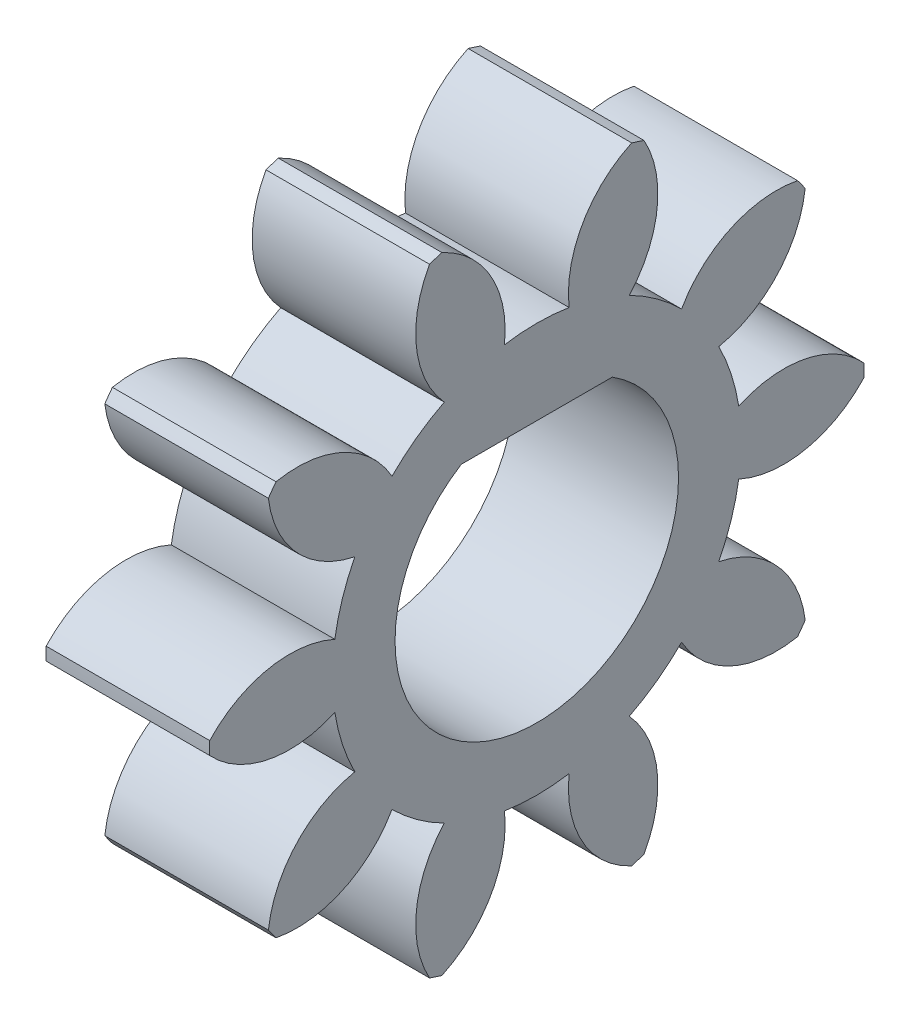
SolidWorks part; units mm, degrees
ref_plane "Plane1" through (0, 0, 0) normal (0, 0, 1) x (1, 0, 0)
ref_plane "Plane2" through (0, 0, 0) normal (0, 1, 0) x (1, 0, 0)
ref_plane "Plane3" through (0, 0, 0) normal (1, 0, 0) x (0, 0, -1)
other "Configuration Table"
sketch "HoldingSke" plane through (0, 0, 0) normal (0, 1, 0) x (1, 0, 0)
  line L0 (0, 0) -> (0.9848, -0.1736)
  line L1 (-15, 0) -> (100, 0) construction
  line L2 (0, 0) -> (-2.1039, 2.3779)
  line L3 (0, 0) -> (-11.863, 4.5341)
  line L4 (0, 0) -> (8.5048, 1.4996)
  line L5 (0, 0) -> (-46.8476, -17.4728)
  line L6 (0, 0) -> (-8.2896, -5.593)
  line L7 (-2.1039, 2.3779) -> (8.6586, 51.2059)
  line L8 (-76.2, 54.61) -> (-75.3, 54.61)
  line L9 (-71.009, 38.7566) -> (-53.1078, 45.2721)
  line L10 (-76.2, 71.12) -> (104.1128, 71.12)
  line L11 (0, 0) -> (-10, 0)
  line L12 (-76.2, 101.6) -> (-76.162, 101.6)
  line L13 (24.9733, 27.94) -> (52.9518, 28.4284)
  line L14 (24.9733, 27.94) -> (24.9743, 27.94)
  line L15 (24.9733, 27.94) -> (100.4006, 29.5858)
  line L16 (-63.627, -1) -> (-12.827, -1)
  circle A0 centre (0, 0) radius 2.5
  circle A1 centre (0, 0) radius 3.749
  circle A2 centre (0, 0) radius 37.5
  circle A3 centre (0, 0) radius 2.5
  dimension "MHD" = 7.498
  dimension "Hub_dia" = 75
  dimension "Bore" = 5
  dimension "MBD" = 5
  dimension "Num_teeth" = 10
  dimension "Pitch" = 1
  dimension "Overall_len" = 50
  dimension "Show_teeth" = 10
  dimension "Thickness" = 10
  dimension "OAL" = 50.0001
  dimension "T_dim" = 0.9
  dimension "Ap" = 20
  dimension "H" = 19.05
  dimension "Pitch_radius" = 180.3128
  dimension "Width" = 10
  dimension "Backlash" = 0.038
  dimension "Addendum_fac" = 1
  dimension "Dedendum_fac" = 1.25
  dimension "Clearance_fac" = 0.25
  dimension "Dedendum_add" = 0.001
  dimension "Module" = 1
sketch "BasProSke" plane through (0, 0, 0) normal (0, 1, 0) x (1, 0, 0)
  line L0 (-10, 0) -> (60, 0) construction
  line L1 (0, 0) -> (0, 6)
  line L2 (0, 0) -> (10, 0)
  line L3 (10, 0) -> (10, 6)
  line L4 (10, 6) -> (0, 6)
  dimension "Thickness" = 10
  dimension "Diameter" = 12
revolve "Base-Revolve" add sketch "BasProSke" angle 360 about L0
sketch "TooCutSke" plane through (0, 0, 0) normal (1, 0, 0) x (0, 0, -1)
  line L1 (0, 0) -> (0, 107) construction
  line L2 (0, 0) -> (-0.8485, 4.9275) construction
  line L3 (0, 0) -> (-3.0584, 9.4126) construction
  line L4 (-0.8485, 4.9275) -> (-1.5292, 4.7063) construction
  arc A0 (0.5928, 3.7018) -> (-0.5928, 3.7018) centre (0, 0) ccw
  arc A1 (1.7758, 5.7578) -> (-1.7758, 5.7578) centre (0, 0) ccw
  circle A2 centre (0, 0) radius 5 construction
  circle A3 centre (0, 0) radius 4.6985 construction
  arc A4 (-0.5928, 3.7018) -> (-1.7758, 5.7578) centre (-2.5801, 3.9267) ccw
  arc A5 (1.7758, 5.7578) -> (0.5928, 3.7018) centre (2.5801, 3.9267) ccw
  dimension "Root_dia" = 7.498
  dimension "Overcut_dia" = 12.0508
  dimension "Pitch_dia" = 10
  dimension "Base_dia" = 9.3969
  dimension "Flank_rad" = 2
  dimension "Half_ang" = 18
  dimension "Half_CT" = 0.7157
extrude "ToothCut" cut sketch "TooCutSke" along normal through all
fillet "Breaks" [suppressed] radius 0.02
fillet "RootFillets" [suppressed] radius 0.251
pattern_circular "TeethCuts" count 10 every 36 about axis through (-10, 0, 0) along (1, 0, 0) of "ToothCut", "RootFillets", "Breaks"
sketch "HubNeaOneSke" plane through (0, 0, 0) normal (-1, 0, 0) x (0, 0, 1)
  circle A0 centre (0, 0) radius 3.749
  dimension "Diameter" = 7.498
extrude "HubNearOne" [suppressed] add sketch "HubNeaOneSke" along normal blind 40.0001
sketch "HubNeaBotSke" plane through (0, 0, 0) normal (-1, 0, 0) x (0, 0, 1)
  circle A0 centre (0, 0) radius 3.749
  dimension "Diameter" = 7.498
extrude "HubNearBoth" [suppressed] add sketch "HubNeaBotSke" along normal blind 20
ref_plane "FarPln" through (10, 0, 0) normal (1, 0, 0) x (0, 0, -1)
sketch "HubFarSke" plane through (10, 0, 0) normal (1, 0, 0) x (0, 0, -1)
  circle A0 centre (0, 0) radius 3.749
  dimension "Diameter" = 7.498
extrude "HubFar" [suppressed] add sketch "HubFarSke" along normal blind 20
sketch "BorSke" plane through (0, 0, 0) normal (1, 0, 0) x (0, 0, -1)
  circle A0 centre (0, 0) radius 2.5
  dimension "Diameter" = 5
extrude "Bore" cut sketch "BorSke" along normal mid plane 100.0001
sketch "KeySke" plane through (0, 0, 0) normal (1, 0, 0) x (0, 0, -1)
  line L0 (-1, 0) -> (-1, 3.4)
  line L1 (-1, 3.4) -> (1, 3.4)
  line L2 (1, 3.4) -> (1, 0)
  line L3 (0, 0) -> (0, 34) construction
  line L4 (-1, 0) -> (1, 0)
  dimension "Offset" = 3.4
  dimension "Width" = 2
extrude "Keyway" [suppressed] cut sketch "KeySke" along normal mid plane 100.0001
pattern_circular "Keyway2" [suppressed] count 2 every 90 about axis through (-10, 0, 0) along (1, 0, 0)
sketch "Sketch1" plane through (10, 0, 0) normal (1, 0, 0) x (0, 0, -1)
  line L0 (0, 0) -> (2.4, 0) construction
  line L1 (2.4, 0.7) -> (2.4, -0.7) construction
  circle A0 centre (0, 0) radius 2.5
  point P7 (2.4, 0)
extrude "Boss-Extrude1" add sketch "Sketch1" against normal blind 10
sketch "Sketch2" plane through (0, 0, 0) normal (-1, 0, 0) x (0, 0, 1)
  line L0 (0, 0) -> (0, 2.2) construction
  line L1 (-1.1874, 2.2) -> (1.1874, 2.2)
  circle A0 centre (0, 0) radius 2.5
  point P7 (0, 2.2)
extrude "Cut-Extrude2" cut sketch "Sketch2" against normal blind 10
sketch "Sketch3" plane through (0, 0, 0) normal (-1, 0, 0) x (0, 0, 1)
  line L0 (-1.3856, 2.2) -> (1.3856, 2.2)
  arc A0 (-1.1874, 2.2) -> (1.1874, 2.2) centre (0, 0) ccw construction
  arc A1 (-1.1874, 2.2) -> (1.1874, 2.2) centre (0, 0) ccw
  arc A2 (-1.3856, 2.2) -> (1.3856, 2.2) centre (0, 0) ccw
  arc A3 (-1.2349, 2.288) -> (1.2349, 2.288) centre (0, 0) ccw construction
  point P9 (0, 2.2)
  dimension "D1" = 0.1
extrude "Cut-Extrude4" cut sketch "Sketch3" against normal blind 12.8 contours A2 L0
sketch "Sketch4" plane through (10, 0, 0) normal (1, 0, 0) x (0, 0, -1)
  arc A40 (5.9988, 0.1189) -> (3.7038, 0.5802) centre (4.5318, -1.2404) ccw
  arc A41 (3.7038, 0.5802) -> (3.3375, 1.7077) centre (0, 0) ccw
  arc A42 (3.3375, 1.7077) -> (4.923, 3.4298) centre (2.9372, 3.6672) ccw
  arc A43 (4.923, 3.4298) -> (4.7833, 3.6222) centre (0, 0) ccw
  arc A44 (4.7833, 3.6222) -> (2.6555, 2.6464) centre (4.3954, 1.6602) ccw
  arc A45 (2.6555, 2.6464) -> (1.6963, 3.3433) centre (0, 0) ccw
  arc A46 (1.6963, 3.3433) -> (1.9668, 5.6685) centre (0.2207, 4.6933) ccw
  arc A47 (1.9668, 5.6685) -> (1.7407, 5.742) centre (0, 0) ccw
  arc A48 (1.7407, 5.742) -> (0.5928, 3.7018) centre (2.5801, 3.9267) ccw
  arc A49 (0.5928, 3.7018) -> (-0.5928, 3.7018) centre (0, 0) ccw
  arc A50 (-0.5928, 3.7018) -> (-1.7407, 5.742) centre (-2.5801, 3.9267) ccw
  arc A51 (-1.7407, 5.742) -> (-1.9668, 5.6685) centre (0, 0) ccw
  arc A52 (-1.9668, 5.6685) -> (-1.6963, 3.3433) centre (-0.2207, 4.6933) ccw
  arc A53 (-1.6963, 3.3433) -> (-2.6555, 2.6464) centre (0, 0) ccw
  arc A54 (-2.6555, 2.6464) -> (-4.7833, 3.6222) centre (-4.3954, 1.6602) ccw
  arc A55 (-4.7833, 3.6222) -> (-4.923, 3.4298) centre (0, 0) ccw
  arc A56 (-4.923, 3.4298) -> (-3.3375, 1.7077) centre (-2.9372, 3.6672) ccw
  arc A57 (-3.3375, 1.7077) -> (-3.7038, 0.5802) centre (0, 0) ccw
  arc A58 (-3.7038, 0.5802) -> (-5.9988, 0.1189) centre (-4.5318, -1.2404) ccw
  arc A59 (-5.9988, 0.1189) -> (-5.9988, -0.1189) centre (0, 0) ccw
  arc A60 (-5.9988, -0.1189) -> (-3.7038, -0.5802) centre (-4.5318, 1.2404) ccw
  arc A61 (-3.7038, -0.5802) -> (-3.3375, -1.7077) centre (0, 0) ccw
  arc A62 (-3.3375, -1.7077) -> (-4.923, -3.4298) centre (-2.9372, -3.6672) ccw
  arc A63 (-4.923, -3.4298) -> (-4.7833, -3.6222) centre (0, 0) ccw
  arc A64 (-4.7833, -3.6222) -> (-2.6555, -2.6464) centre (-4.3954, -1.6602) ccw
  arc A65 (-2.6555, -2.6464) -> (-1.6963, -3.3433) centre (0, 0) ccw
  arc A66 (-1.6963, -3.3433) -> (-1.9668, -5.6685) centre (-0.2207, -4.6933) ccw
  arc A67 (-1.9668, -5.6685) -> (-1.7407, -5.742) centre (0, 0) ccw
  arc A68 (-1.7407, -5.742) -> (-0.5928, -3.7018) centre (-2.5801, -3.9267) ccw
  arc A69 (-0.5928, -3.7018) -> (0.5928, -3.7018) centre (0, 0) ccw
  arc A70 (0.5928, -3.7018) -> (1.7407, -5.742) centre (2.5801, -3.9267) ccw
  arc A71 (1.7407, -5.742) -> (1.9668, -5.6685) centre (0, 0) ccw
  arc A72 (1.9668, -5.6685) -> (1.6963, -3.3433) centre (0.2207, -4.6933) ccw
  arc A73 (1.6963, -3.3433) -> (2.6555, -2.6464) centre (0, 0) ccw
  arc A74 (2.6555, -2.6464) -> (4.7833, -3.6222) centre (4.3954, -1.6602) ccw
  arc A75 (4.7833, -3.6222) -> (4.923, -3.4298) centre (0, 0) ccw
  arc A76 (4.923, -3.4298) -> (3.3375, -1.7077) centre (2.9372, -3.6672) ccw
  arc A77 (3.3375, -1.7077) -> (3.7038, -0.5802) centre (0, 0) ccw
  arc A78 (3.7038, -0.5802) -> (5.9988, -0.1189) centre (4.5318, 1.2404) ccw
  arc A79 (5.9988, -0.1189) -> (5.9988, 0.1189) centre (0, 0) ccw
  arc A80 (5.9988, 0.1189) -> (3.7038, 0.5802) centre (4.5318, -1.2404) ccw
  arc A81 (3.7038, 0.5802) -> (3.3375, 1.7077) centre (0, 0) ccw
  arc A82 (3.3375, 1.7077) -> (4.923, 3.4298) centre (2.9372, 3.6672) ccw
  arc A83 (4.923, 3.4298) -> (4.7833, 3.6222) centre (0, 0) ccw
  arc A84 (4.7833, 3.6222) -> (2.6555, 2.6464) centre (4.3954, 1.6602) ccw
  arc A85 (2.6555, 2.6464) -> (1.6963, 3.3433) centre (0, 0) ccw
  arc A86 (1.6963, 3.3433) -> (1.9668, 5.6685) centre (0.2207, 4.6933) ccw
  arc A87 (1.9668, 5.6685) -> (1.7407, 5.742) centre (0, 0) ccw
  arc A88 (1.7407, 5.742) -> (0.5928, 3.7018) centre (2.5801, 3.9267) ccw
  arc A89 (0.5928, 3.7018) -> (-0.5928, 3.7018) centre (0, 0) ccw
  arc A90 (-0.5928, 3.7018) -> (-1.7407, 5.742) centre (-2.5801, 3.9267) ccw
  arc A91 (-1.7407, 5.742) -> (-1.9668, 5.6685) centre (0, 0) ccw
  arc A92 (-1.9668, 5.6685) -> (-1.6963, 3.3433) centre (-0.2207, 4.6933) ccw
  arc A93 (-1.6963, 3.3433) -> (-2.6555, 2.6464) centre (0, 0) ccw
  arc A94 (-2.6555, 2.6464) -> (-4.7833, 3.6222) centre (-4.3954, 1.6602) ccw
  arc A95 (-4.7833, 3.6222) -> (-4.923, 3.4298) centre (0, 0) ccw
  arc A96 (-4.923, 3.4298) -> (-3.3375, 1.7077) centre (-2.9372, 3.6672) ccw
  arc A97 (-3.3375, 1.7077) -> (-3.7038, 0.5802) centre (0, 0) ccw
  arc A98 (-3.7038, 0.5802) -> (-5.9988, 0.1189) centre (-4.5318, -1.2404) ccw
  arc A99 (-5.9988, 0.1189) -> (-5.9988, -0.1189) centre (0, 0) ccw
  arc A100 (-5.9988, -0.1189) -> (-3.7038, -0.5802) centre (-4.5318, 1.2404) ccw
  arc A101 (-3.7038, -0.5802) -> (-3.3375, -1.7077) centre (0, 0) ccw
  arc A102 (-3.3375, -1.7077) -> (-4.923, -3.4298) centre (-2.9372, -3.6672) ccw
  arc A103 (-4.923, -3.4298) -> (-4.7833, -3.6222) centre (0, 0) ccw
  arc A104 (-4.7833, -3.6222) -> (-2.6555, -2.6464) centre (-4.3954, -1.6602) ccw
  arc A105 (-2.6555, -2.6464) -> (-1.6963, -3.3433) centre (0, 0) ccw
  arc A106 (-1.6963, -3.3433) -> (-1.9668, -5.6685) centre (-0.2207, -4.6933) ccw
  arc A107 (-1.9668, -5.6685) -> (-1.7407, -5.742) centre (0, 0) ccw
  arc A108 (-1.7407, -5.742) -> (-0.5928, -3.7018) centre (-2.5801, -3.9267) ccw
  arc A109 (-0.5928, -3.7018) -> (0.5928, -3.7018) centre (0, 0) ccw
  arc A110 (0.5928, -3.7018) -> (1.7407, -5.742) centre (2.5801, -3.9267) ccw
  arc A111 (1.7407, -5.742) -> (1.9668, -5.6685) centre (0, 0) ccw
  arc A112 (1.9668, -5.6685) -> (1.6963, -3.3433) centre (0.2207, -4.6933) ccw
  arc A113 (1.6963, -3.3433) -> (2.6555, -2.6464) centre (0, 0) ccw
  arc A114 (2.6555, -2.6464) -> (4.7833, -3.6222) centre (4.3954, -1.6602) ccw
  arc A115 (4.7833, -3.6222) -> (4.923, -3.4298) centre (0, 0) ccw
  arc A116 (4.923, -3.4298) -> (3.3375, -1.7077) centre (2.9372, -3.6672) ccw
  arc A117 (3.3375, -1.7077) -> (3.7038, -0.5802) centre (0, 0) ccw
  arc A118 (3.7038, -0.5802) -> (5.9988, -0.1189) centre (4.5318, 1.2404) ccw
  arc A119 (5.9988, -0.1189) -> (5.9988, 0.1189) centre (0, 0) ccw
  dimension "D1" = 0
extrude "Cut-Extrude5" cut sketch "Sketch4" against normal blind 7 contours A80 A81 A82 A83 A84 A85 A86 A87 A88 A89 A90 A91 A92 A93 A94 A95 A96 A97 A98 A99 A100 A101 A102 A103 A104 A105 A106 A107 A108 A109 A110 A111 A112 A113 A114 A115 A116 A117 A118 A119
equation "' \"Module@HoldingSke\" = 6.35"
equation "' \"Num_teeth@HoldingSke\" = 12"
equation "' \"Ap@HoldingSke\" =  20"
equation "' \"Ap@HoldingSke\" = 20"
equation "' \"Width@HoldingSke\" = 0.5 * 25.4"
equation "' \"Hub_dia@HoldingSke\"= 1 * 25.4"
equation "' \"Hub_dia@HoldingSke\" = 1 * 25.4"
equation "' \"Overall_len@HoldingSke\" = 1.0 * 25.4"
equation "' \"Bore@HoldingSke\" = 0.75 * 25.4"
equation "' \"T_dim@HoldingSke\" = 0.1 * 25.4"
equation "' \"Width@KeySke\" = 0.25 * 25.4"
equation "' \"Show_teeth@HoldingSke\" = 13"
equation "' \"Backlash@HoldingSke\" = 0.009 * 25.4"
equation "' \"Addendum_fac@HoldingSke\" = 1.0"
equation "' \"Dedendum_fac@HoldingSke\" = 1.25"
equation "' \"Dedendum_add@HoldingSke\" = 0.00005 * 25.4"
equation "' \"Clearance_fac@HoldingSke\" = 0.25"
equation "\"Pitch@HoldingSke\" = 1 / \"Module@HoldingSke\""
equation "\"Overcut_dia@TooCutSke\" = (\"Num_teeth@HoldingSke\" + 2 * \"Addendum_fac@HoldingSke\") / \"Pitch@HoldingSke\" + 0.002 * 25.4"
equation "\"Pitch_dia@TooCutSke\" = \"Num_teeth@HoldingSke\" / \"Pitch@HoldingSke\""
equation "\"Base_dia@TooCutSke\" = \"Num_teeth@HoldingSke\" / \"Pitch@HoldingSke\" * cos((\"Ap@HoldingSke\"  * 3.14159265 / 180))"
equation "\"Root_dia@TooCutSke\" = (\"Num_teeth@HoldingSke\" + 2) / \"Pitch@HoldingSke\" - 2 * (\"Addendum_fac@HoldingSke\" + \"Dedendum_fac@HoldingSke\") / \"Pitch@HoldingSke\" - \"Dedendum_add@HoldingSke\" * 2"
equation "\"Half_ang@TooCutSke\" = 180 / \"Num_teeth@HoldingSke\""
equation "\"Half_CT@TooCutSke\" = \"Num_teeth@HoldingSke\" / \"Pitch@HoldingSke\" * sin((3.14159265 / 2 / \"Num_teeth@HoldingSke\")) / 2 - 7 * \"Backlash@HoldingSke\" / 4"
equation "\"Flank_rad@TooCutSke\" = \"Num_teeth@HoldingSke\" / \"Pitch@HoldingSke\" / 5"
equation "\"Radius@RootFillets\" = \"Clearance_fac@HoldingSke\" / \"Pitch@HoldingSke\" + \"Dedendum_add@HoldingSke\""
equation "\"Break_rad@Breaks\" = 0.02 / \"Pitch@HoldingSke\""
equation "\"Thickness@HoldingSke\" = \"Width@HoldingSke\""
equation "\"OAL@HoldingSke\" = \"Thickness@HoldingSke\""
equation "\"MHD@HoldingSke\" = (\"Num_teeth@HoldingSke\" + 2) / \"Pitch@HoldingSke\" - 2 * (\"Addendum_fac@HoldingSke\" + \"Dedendum_fac@HoldingSke\")  / \"Pitch@HoldingSke\" - \"Dedendum_add@HoldingSke\" * 2"
equation "\"MBD@HoldingSke\" = (\"Num_teeth@HoldingSke\" + 2) / \"Pitch@HoldingSke\" - 2 * (\"Addendum_fac@HoldingSke\" + \"Dedendum_fac@HoldingSke\")  / \"Pitch@HoldingSke\" - \"Dedendum_add@HoldingSke\" * 2 - 0.002 * 25.4"
equation "\"MHD@HoldingSke\" = ((sgn( \"MHD@HoldingSke\" - \"Hub_dia@HoldingSke\" )-1)*( \"MHD@HoldingSke\" - \"Hub_dia@HoldingSke\" ))/-2+ \"Hub_dia@HoldingSke\""
equation "\"MBD@HoldingSke\" = ((sgn( \"MBD@HoldingSke\" - \"Bore@HoldingSke\" )-1)*( \"MBD@HoldingSke\" - \"Bore@HoldingSke\" ))/-2+ \"Bore@HoldingSke\""
equation "\"OAL@HoldingSke\" = ((sgn( \"OAL@HoldingSke\" - \"Overall_len@HoldingSke\" )+1)*( \"OAL@HoldingSke\" - \"Overall_len@HoldingSke\" ))/2 + \"Overall_len@HoldingSke\" + 0.000002 * 25.4"
equation "\"Num_teeth@TeethCuts\" = int( \"Show_teeth@HoldingSke\" ) + 1"
equation "\"Num_teeth@TeethCuts\" = ((sgn( \"Num_teeth@TeethCuts\" - \"Num_teeth@HoldingSke\" )-1)*( \"Num_teeth@TeethCuts\" - \"Num_teeth@HoldingSke\" ))/-2+ \"Num_teeth@HoldingSke\""
equation "\"Num_teeth@TeethCuts\" = ((sgn( \"Num_teeth@TeethCuts\" - 2.0)+1)*( \"Num_teeth@TeethCuts\" - 2.0))/2 +2.0"
equation "\"Angle@TeethCuts\" = 360.0 / \"Num_teeth@HoldingSke\""
equation "\"Diameter@BasProSke\" = (\"Num_teeth@HoldingSke\" + 2 * \"Addendum_fac@HoldingSke\") / \"Pitch@HoldingSke\""
equation "\"Thickness@BasProSke\"  = \"Thickness@HoldingSke\""
equation "' \"Fillet_rad@BasProSke\" =  \"Thickness@HoldingSke\" * 0.05"
equation "' \"Fillet_rad@BasProSke\" = \"Thickness@HoldingSke\" * 0.05"
equation "\"MHD@HoldingSke\" = ((sgn( \"MHD@HoldingSke\" - \"Root_dia@TooCutSke\" )-1)*( \"MHD@HoldingSke\" - \"Root_dia@TooCutSke\" ))/-2+ \"Root_dia@TooCutSke\""
equation "\"Diameter@HubNeaOneSke\" = \"MHD@HoldingSke\""
equation "\"Length@HubNearOne\" = \"OAL@HoldingSke\" - \"Thickness@BasProSke\""
equation "\"Diameter@HubNeaBotSke\" = \"MHD@HoldingSke\""
equation "\"Length@HubNearBoth\" = ( \"OAL@HoldingSke\" - \"Thickness@BasProSke\" ) / 2.0"
equation "\"Thickness@FarPln\" = \"Thickness@BasProSke\""
equation "\"Diameter@HubFarSke\" = \"MHD@HoldingSke\""
equation "\"Length@HubFar\" = ( \"OAL@HoldingSke\" - \"Thickness@BasProSke\" ) / 2.0"
equation "\"Diameter@BorSke\" = \"MBD@HoldingSke\""
equation "\"D1@Bore\" = \"OAL@HoldingSke\" * 2.0"
equation "\"D1@Keyway\" = \"OAL@HoldingSke\" * 2.0"
equation "\"Offset@KeySke\" = \"T_dim@HoldingSke\" + \"MBD@HoldingSke\" / 2.0"
